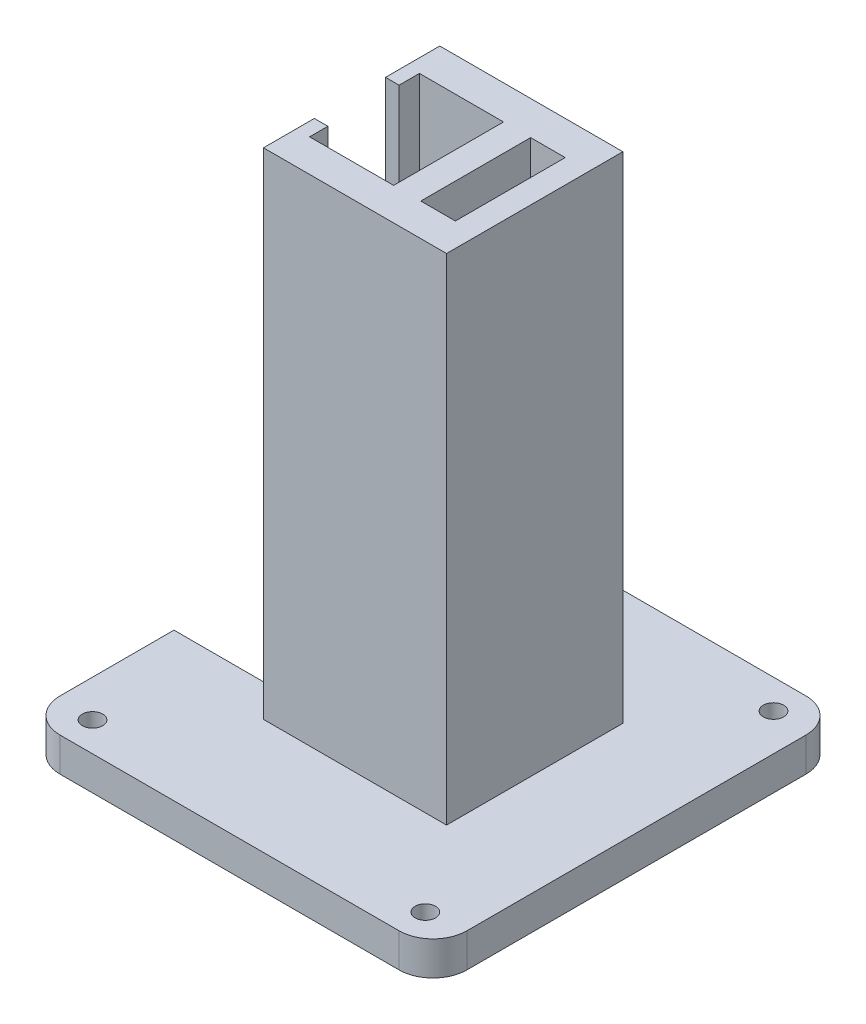
SolidWorks part; units mm, degrees
ref_plane "Front Plane" through (0, 0, 0) normal (0, 0, 1) x (1, 0, 0)
ref_plane "Top Plane" through (0, 0, 0) normal (0, 1, 0) x (1, 0, 0)
ref_plane "Right Plane" through (0, 0, 0) normal (1, 0, 0) x (0, 0, -1)
sketch "Sketch1" plane through (0, 0, 0) normal (0, 0, 1) x (1, 0, 0)
  line L1 (15, -36.5) -> (-15, -36.5)
  line L2 (15, -36.5) -> (15, 36.5)
  line L3 (15, 36.5) -> (-15, 36.5)
  line L4 (-15, -36.5) -> (-15, 36.5)
  line L5 (15, -36.5) -> (-15, 36.5) construction
  line L6 (15, 36.5) -> (-15, -36.5) construction
  point P0 (0, 0)
  dimension "D1" = 30
  dimension "D2" = 73
extrude "Boss-Extrude1" add sketch "Sketch1" along normal blind 26
sketch "Sketch2" plane through (0, 36.5, 0) normal (0, 1, 0) x (1, 0, 0)
  line L0 (-15, -26) -> (-15, 0) construction
  line L1 (-13.5, -5) -> (11.5, -5)
  line L2 (-13.5, -5) -> (-13.5, -21.2)
  line L3 (-13.5, -21.2) -> (11.5, -21.2)
  line L4 (11.5, -5) -> (11.5, -21.2)
  line L5 (15, 0) -> (-15, 0) construction
  line L6 (15, -26) -> (15, 0) construction
  dimension "D1" = 1.5
  dimension "D2" = 5
  dimension "D3" = 16.2
  dimension "D4" = 3.5
extrude "Cut-Extrude1" cut sketch "Sketch2" against normal through all
sketch "Sketch3" plane through (-15, 0, 0) normal (-1, 0, 0) x (0, 0, 1)
  line L0 (0, 36.5) -> (0, -36.5) construction
  line L1 (0, 33.5) -> (26, 33.5)
  line L2 (0, 33.5) -> (0, 9.5)
  line L3 (0, 9.5) -> (26, 9.5)
  line L4 (26, 33.5) -> (26, 9.5)
  line L5 (26, 36.5) -> (26, -36.5) construction
  line L6 (26, 36.5) -> (0, 36.5) construction
  line L8 (0, 6.5) -> (26, 6.5)
  line L9 (0, 6.5) -> (0, -17.5)
  line L10 (0, -17.5) -> (26, -17.5)
  line L11 (26, 6.5) -> (26, -17.5)
  line L12 (0, -20.5) -> (26, -20.5)
  line L13 (0, -20.5) -> (0, -36.7342)
  line L14 (0, -36.7342) -> (26, -36.7342)
  line L15 (26, -20.5) -> (26, -36.7342)
  dimension "D1" = 3
  dimension "D2" = 24
  dimension "D3" = 3
  dimension "D4" = 3
  dimension "D5" = 24
extrude "Cut-Extrude2" cut sketch "Sketch3" against normal blind 5
ref_plane "Plane1" through (0, -36.5, 0) normal (0, -1, 0) x (-1, 0, 0)
sketch "Sketch5" plane through (0, -36.5, 0) normal (0, -1, 0) x (-1, 0, 0)
  line L0 (0, 0) -> (0, -31.2349) construction
  line L1 (-15, -13) -> (15, -13) construction
  line L2 (-15, -26) -> (-15, 0) construction
  line L3 (15, -26) -> (15, 0) construction
  line L5 (30, -43) -> (-30, -43)
  line L6 (30, -43) -> (30, 17)
  line L7 (30, 17) -> (-30, 17)
  line L8 (-30, -43) -> (-30, 17)
  line L9 (30, -43) -> (-30, 17) construction
  line L10 (30, 17) -> (-30, -43) construction
  point P9 (0, -13)
  dimension "D1" = 60
  dimension "D2" = 60
extrude "Boss-Extrude2" add sketch "Sketch5" along normal blind 5
fillet "Fillet1" radius 5 4 edges at (-30, -39, -17) (30, -39, -17) (30, -39, 43) (-30, -39, 43)
sketch "Sketch6" plane through (0, -36.5, 0) normal (0, 1, 0) x (1, 0, 0)
  line L0 (0, 17) -> (0, -43) construction
  line L1 (-25, 17) -> (25, 17) construction
  line L2 (25, -43) -> (-25, -43) construction
  line L3 (-30, -13) -> (43.9834, -13) construction
  line L4 (-30, -38) -> (-30, 12) construction
  circle A0 centre (-24.5405, 12.6715) radius 1.5
  circle A1 centre (24.5405, 12.6715) radius 1.5
  circle A2 centre (-24.5405, -38.6715) radius 1.5
  circle A3 centre (24.5405, -38.6715) radius 1.5
  dimension "D1" = 3
extrude "Cut-Extrude4" cut sketch "Sketch6" against normal blind 5
sketch "Sketch7" plane through (0, 0, 0) normal (0, 0, -1) x (-1, 0, 0)
  line L0 (-15, 36.5) -> (15, 36.5) construction
  line L1 (-15, -36.5) -> (-15, 36.5) construction
  circle A0 centre (-7, 31.5) radius 1
  circle A1 centre (-12, 24.5) radius 1
  circle A2 centre (-2, 24.5) radius 1
  circle A3 centre (-7, 18.5) radius 1
  dimension "D1" = 2
  dimension "D2" = 5
  dimension "D4" = 2
  dimension "D7" = 2
  dimension "D8" = 12
  dimension "D9" = 13
  dimension "D10" = 2
  dimension "D3" = 8
  dimension "D5" = 12
  dimension "D6" = 3
  dimension "D11" = 8
  dimension "D12" = 18
extrude "Cut-Extrude5" cut sketch "Sketch7" against normal blind 4
sketch "Sketch8" plane through (-30, 0, 0) normal (-1, 0, 0) x (0, 0, 1)
  line L0 (38, -41.5) -> (-12, -41.5) construction
  line L1 (5, -36.5) -> (20.5, -36.5)
  line L2 (5, -36.5) -> (5, -41.5)
  line L3 (5, -41.5) -> (20.5, -41.5)
  line L4 (20.5, -36.5) -> (20.5, -41.5)
  line L5 (38, -36.5) -> (-12, -36.5) construction
  line L6 (21.2, -36.5) -> (5, -36.5) construction
extrude "Cut-Extrude6" cut sketch "Sketch8" against normal blind 42
sketch "Sketch9" plane through (0, 36.5, 0) normal (0, 1, 0) x (1, 0, 0)
  line L0 (15, -26) -> (-15, -26) construction
  line L1 (-15, 0) -> (-10, 0)
  line L2 (-15, 0) -> (-15, -26)
  line L3 (-15, -26) -> (-10, -26)
  line L4 (-10, 0) -> (-10, -26)
  dimension "D1" = 5
extrude "Cut-Extrude7" cut sketch "Sketch9" against normal blind 73
ref_plane "Plane2" through (0, 36.5, 0) normal (0, 1, 0) x (1, 0, 0)
sketch "Sketch10" plane through (0, 36.5, 0) normal (0, 1, 0) x (1, 0, 0)
  line L0 (-10, 0) -> (-12, 0)
  line L1 (15, 0) -> (-15, 0) construction
  line L2 (-12, 0) -> (-12, -8)
  line L3 (-12, -8) -> (-10, -8)
  line L4 (-10, -8) -> (-10, 0)
  line L5 (-10, -26) -> (-12, -26)
  line L6 (-12, -26) -> (-12, -18.5)
  line L7 (-12, -18.5) -> (-10, -18.5)
  line L8 (-10, -18.5) -> (-10, -26)
  dimension "D1" = 2
  dimension "D2" = 8
  dimension "D3" = 2
  dimension "D4" = 7.5
extrude "Boss-Extrude3" add sketch "Sketch10" against normal blind 78
sketch "Sketch11" plane through (0, -36.5, 0) normal (0, 1, 0) x (1, 0, 0)
  line L0 (11.5, -20.5) -> (11.5, -21.2)
  line L1 (11.5, -21.2) -> (-30, -21.2)
  line L2 (-30, -38) -> (-30, -20.5) construction
  line L3 (-30, -21.2) -> (-30, -20.5)
  line L4 (-30, -20.5) -> (11.5, -20.5)
extrude "Cut-Extrude8" cut sketch "Sketch11" against normal through all
ref_plane "Plane4" through (-12, 0, 0) normal (-1, 0, 0) x (0, 0, 1)
sketch "Sketch13" plane through (-12, 0, 0) normal (-1, 0, 0) x (0, 0, 1)
  line L0 (20.5, -36.5) -> (21.2, -36.5)
  line L1 (21.2, -36.5) -> (21.2, -41.5)
  line L2 (21.2, -41.5) -> (20.5, -41.5)
  line L3 (20.5, -41.5) -> (20.5, -36.5)
extrude "Boss-Extrude5" add sketch "Sketch13" against normal blind 2
sketch "Sketch15" plane through (0, 36.5, 0) normal (0, 1, 0) x (1, 0, 0)
  line L0 (2.4, -5) -> (2.4, -21.2)
  line L1 (11.5, -5) -> (-10, -5) construction
  line L2 (-10, -21.2) -> (11.5, -21.2) construction
  line L3 (2.4, -21.2) -> (6.4, -21.2)
  line L5 (6.4, -5) -> (2.4, -5)
  line L6 (6.4, -5) -> (6.4, -21.2)
  dimension "D1" = 12.4
  dimension "D2" = 4
extrude "Boss-Extrude6" add sketch "Sketch15" against normal blind 78
